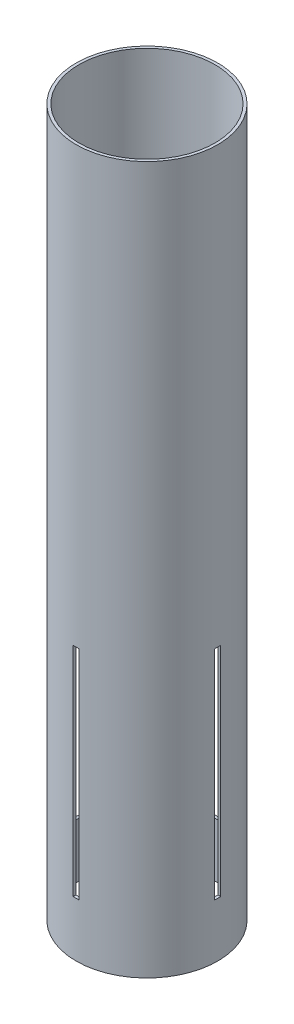
SolidWorks part; units mm, degrees
ref_plane "Front Plane" through (0, 0, 0) normal (0, 0, 1) x (1, 0, 0)
ref_plane "Top Plane" through (0, 0, 0) normal (0, 1, 0) x (1, 0, 0)
ref_plane "Right Plane" through (0, 0, 0) normal (1, 0, 0) x (0, 0, -1)
sketch "Sketch1" plane through (0, 0, 0) normal (0, 1, 0) x (1, 0, 0)
  circle A0 centre (0, 0) radius 39.6748
  circle A1 centre (0, 0) radius 38.1
  dimension "D1" = 79.3496
  dimension "D2" = 76.2
extrude "Boss-Extrude1" add sketch "Sketch1" along normal mid plane 396.24
sketch "Sketch2" plane through (0, 0, 0) normal (1, 0, 0) x (0, 0, -1)
  line L0 (0, 198.12) -> (0, -198.12)
  line L1 (-1.6828, -45.72) -> (1.6827, -45.72)
  line L2 (-1.6828, -45.72) -> (-1.6827, -167.64)
  line L3 (-1.6827, -167.64) -> (1.6828, -167.64)
  line L4 (1.6827, -45.72) -> (1.6828, -167.64)
  line L5 (39.6748, 198.12) -> (-39.6748, 198.12) construction
  line L6 (-39.6748, -198.12) -> (39.6748, -198.12) construction
  line L7 (39.6748, -198.12) -> (39.6748, 198.12) construction
  dimension "D1" = 121.92
  dimension "D2" = 3.3655
  dimension "D3" = 30.48
  dimension "D4" = 37.9921
extrude "Cut-Extrude1" cut sketch "Sketch2" against normal through all both and the other way through all contours L4 L3 L2 L1
pattern_circular "CirPattern2" count 2 over 90 about axis through (0, 198.12, 0) along (0, -1, 0) of "Cut-Extrude1"
equation "\"iDiameter\"= 3in"
equation "\"oDiameter\"= 3.124in"
equation "\"length\"= 15.6in"
equation "\"D1@Sketch1\"=\"oDiameter\""
equation "\"D2@Sketch1\"=\"iDiameter\""
equation "\"D1@Boss-Extrude1\"=\"length\""
